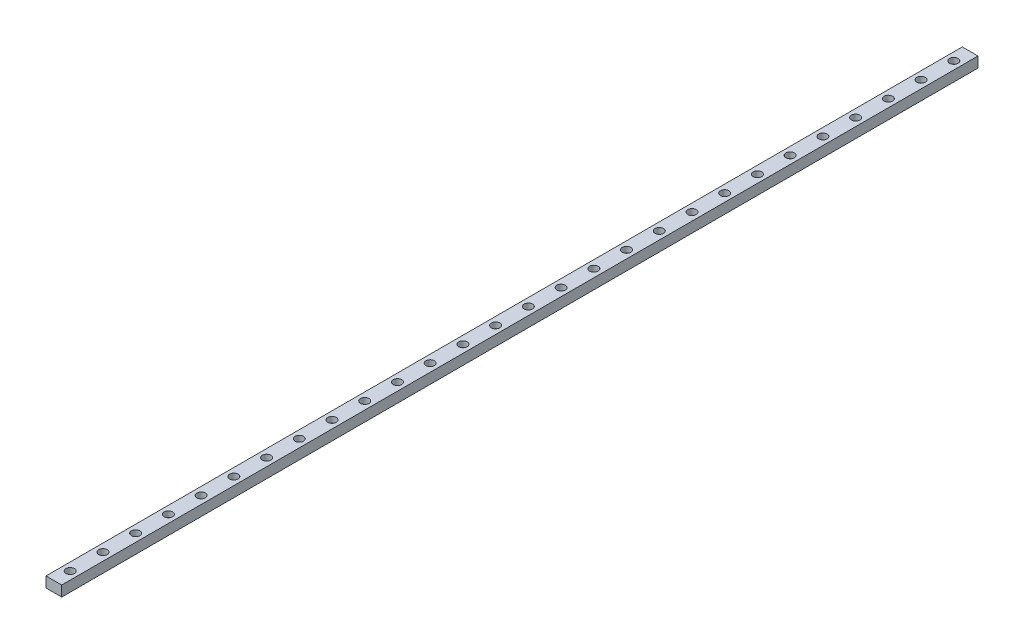
SolidWorks part; units mm, degrees
ref_plane "Front" through (0, 0, 0) normal (0, 0, 1) x (1, 0, 0)
ref_plane "Top" through (0, 0, 0) normal (0, 1, 0) x (1, 0, 0)
ref_plane "Right" through (0, 0, 0) normal (1, 0, 0) x (0, 0, -1)
sketch "Sketch1" plane through (0, 0, 0) normal (0, 0, 1) x (1, 0, 0)
  line L1 (0, 0) -> (12, 0)
  line L2 (0, 0) -> (0, 8)
  line L3 (0, 8) -> (12, 8)
  line L4 (12, 0) -> (12, 8)
  dimension "D1" = 12
  dimension "D2" = 8
extrude "Boss-Extrude1" add sketch "Sketch1" along normal blind 700
hole_wizard "CBORE for M3 SHCS1" positions "Sketch2" profile "Sketch3" counterbore size "M3" standard "ANSI Metric" end condition through all
sketch "Sketch2" plane through (0, 8, 0) normal (0, 1, 0) x (1, 0, 0)
  line L0 (12, -700) -> (0, -700) construction
  point P0 (6, -687.5)
  point P11 (6, -662.5)
  point P12 (6, -637.5)
  point P13 (6, -612.5)
  point P14 (6, -587.5)
  point P15 (6, -562.5)
  point P16 (6, -537.5)
  point P17 (6, -512.5)
  point P18 (6, -487.5)
  point P19 (6, -462.5)
  point P20 (6, -437.5)
  point P21 (6, -412.5)
  point P22 (6, -387.5)
  point P23 (6, -362.5)
  point P24 (6, -337.5)
  point P25 (6, -312.5)
  point P26 (6, -287.5)
  point P27 (6, -262.5)
  point P32 (6, -237.5)
  point P33 (6, -212.5)
  point P34 (6, -187.5)
  point P35 (6, -162.5)
  point P36 (6, -137.5)
  point P37 (6, -112.5)
  point P38 (6, -87.5)
  point P39 (6, -62.5)
  point P40 (6, -37.5)
  point P41 (6, -12.5)
  point P45 (0, 0)
  dimension "D1" = 12.5
  dimension "D2" = 28
sketch "Sketch3" plane through (6, 8, 687.5) normal (1, 0, 0) x (0, 0, 1)
  line L0 (0, 0) -> (0, 8)
  line L1 (0, 8) -> (1.7, 8)
  line L3 (1.7, 8) -> (1.7, 4.5)
  line L4 (1.7, 4.5) -> (3.25, 4.5)
  line L5 (3.25, 4.5) -> (3.25, 0)
  line L7 (3.25, 0) -> (0, 0)
  line L11 (0, -6.35) -> (0, 107.95) construction
  dimension "Thru Hole Dia." = 3.4
  dimension "Thru Hole Depth" = 8
  dimension "C'Bore Dia." = 6.5
  dimension "C'Bore Depth" = 4.5
equation "\"length\"=700"
equation "\"D1@Boss-Extrude1\"= \"length\""
